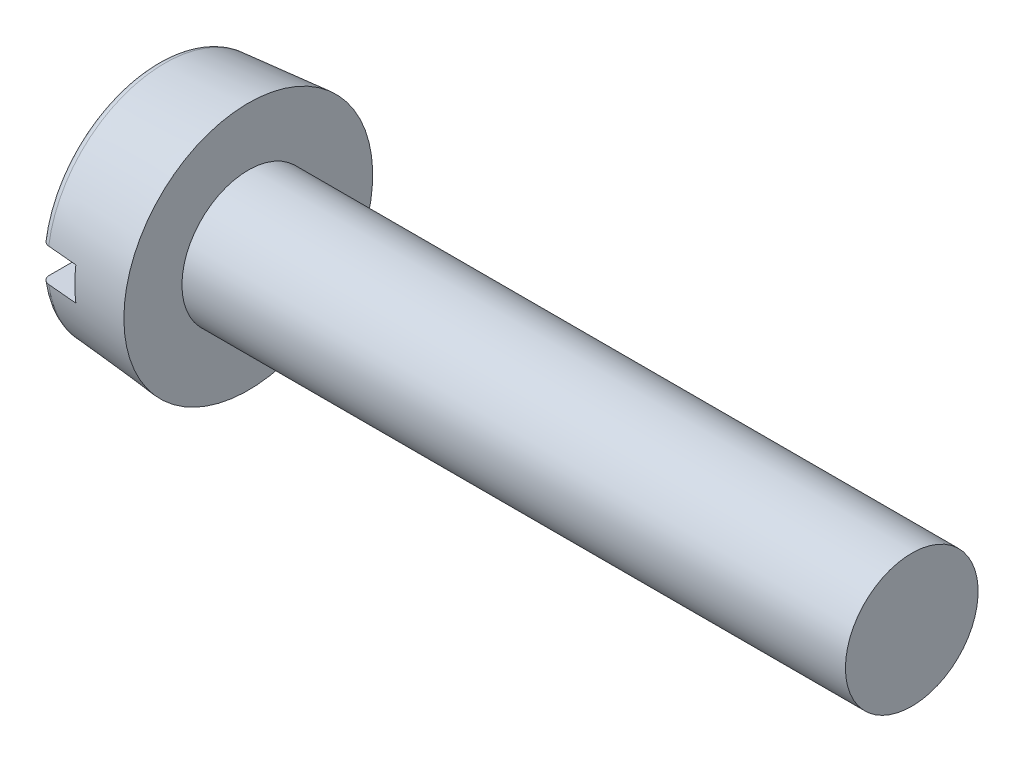
SolidWorks part; units mm, degrees
ref_plane "Plane1" through (0, 0, 0) normal (0, 0, 1) x (1, 0, 0)
ref_plane "Plane2" through (0, 0, 0) normal (0, 1, 0) x (1, 0, 0)
ref_plane "Plane3" through (0, 0, 0) normal (1, 0, 0) x (0, 0, -1)
sketch "BodySke" plane through (0, 0, 0) normal (0, 0, 1) x (1, 0, 0)
  line L0 (1.1, 0.8) -> (1.1, 1.5)
  line L1 (0, 0) -> (0, 1.4038)
  line L2 (-25.4, 0) -> (127, 0) construction
  line L3 (9.1, 0) -> (0, 0)
  line L4 (1.1, 0.8) -> (9.1, 0.8)
  line L5 (9.1, 0.8) -> (9.1, 0)
  line L6 (0, 1.4038) -> (1.1, 1.5)
  line L9 (1.45, 2.3875) -> (1.45, -7.1375) construction
  line L10 (1.1, 6.35) -> (1.1, -3.175) construction
  dimension "Length" = 8
  dimension "Head_ht" = 1.1
  dimension "Advance" = 0.35
  dimension "Thread_nom" = 8
  dimension "Head_dia" = 3
  dimension "Head_side_angle" = 5
  dimension "Diameter" = 1.6
revolve "Base-Revolve" add sketch "BodySke"
cosmetic thread "ThreadCosmetic" [suppressed]
fillet "Fillet1" [suppressed] radius 0.1
fillet "Fillet2" radius 0.1 1 edges at (0, 0, 1.4038)
sketch "Sketch2" plane through (0, 0, 0) normal (1, 0, 0) x (0, 0, -1)
  line L0 (1.5, -0.2) -> (-1.5, -0.2)
  line L1 (1.5, -0.2) -> (1.5, 0.2)
  line L2 (-1.5, 0.2) -> (1.5, 0.2)
  line L3 (-1.5, 0.2) -> (-1.5, -0.2)
  dimension "D1" = 3
  dimension "Slot_width" = 0.4
  dimension "D2" = 1.5
  dimension "D3" = 0.2
extrude "Slot" cut sketch "Sketch2" along normal blind 0.45
sketch "ThdSchSke" plane through (0, 0, 0) normal (0, 0, 1) x (1, 0, 0)
  line L0 (1.8, -0.601) -> (1.6607, -0.8)
  line L1 (1.8, -0.601) -> (1.9393, -0.8)
  line L2 (1.9393, -0.8) -> (1.9393, -1)
  line L3 (-3.175, 0) -> (5.1513, 0) construction
  line L5 (1.9393, -1) -> (1.6607, -1)
  line L6 (1.6607, -1) -> (1.6607, -0.8)
  dimension "Diameter" = 1.6
  dimension "SideAngle" = 55
  dimension "VeeAngle" = 70
  dimension "Thread_minor" = 1.202
  dimension "Overcut" = 2
  dimension "Start" = 1.8
revolve "ThreadSchematic" [suppressed] cut sketch "ThdSchSke" angle 360 about L3
pattern_linear "ThdSchPat" [suppressed]
equation "\"D1@Sketch2\" = \"Head_dia@BodySke\""
equation "\"D2@Sketch2\" = \"D1@Sketch2\" / 2"
equation "\"D3@Sketch2\" = \"Slot_width@Sketch2\" / 2"
equation "\"Thread_length@ThreadCosmetic\" = ((sgn( (\"Length@BodySke\" - \"Advance@BodySke\" * 2.0 ) - \"Thread_nom@BodySke\" )-1)*( (\"Length@BodySke\" - \"Advance@BodySke\"  * 2.0) - \"Thread_nom@BodySke\" ))/-2+ \"Thread_nom@BodySke\""
equation "\"Thread_minor@ThdSchSke\" = \"Thread_minor@ThreadCosmetic\""
equation "\"Diameter@ThdSchSke\" = \"Diameter@BodySke\""
equation "\"Overcut@ThdSchSke\" = \"Diameter@BodySke\" * 1.25"
equation "\"Start@ThdSchSke\" = \"Head_ht@BodySke\" + \"Length@BodySke\" - \"Thread_length@ThreadCosmetic\"  '---Non-countersunk---"
equation "\"Num_threads@ThdSchPat\" = int( \"Thread_length@ThreadCosmetic\" / \"Advance@BodySke\" + 0.999 )  + 1"
equation "\"Advance@ThdSchPat\" = \"Thread_length@ThreadCosmetic\" /  (\"Num_threads@ThdSchPat\" - 1) 'relax it"
